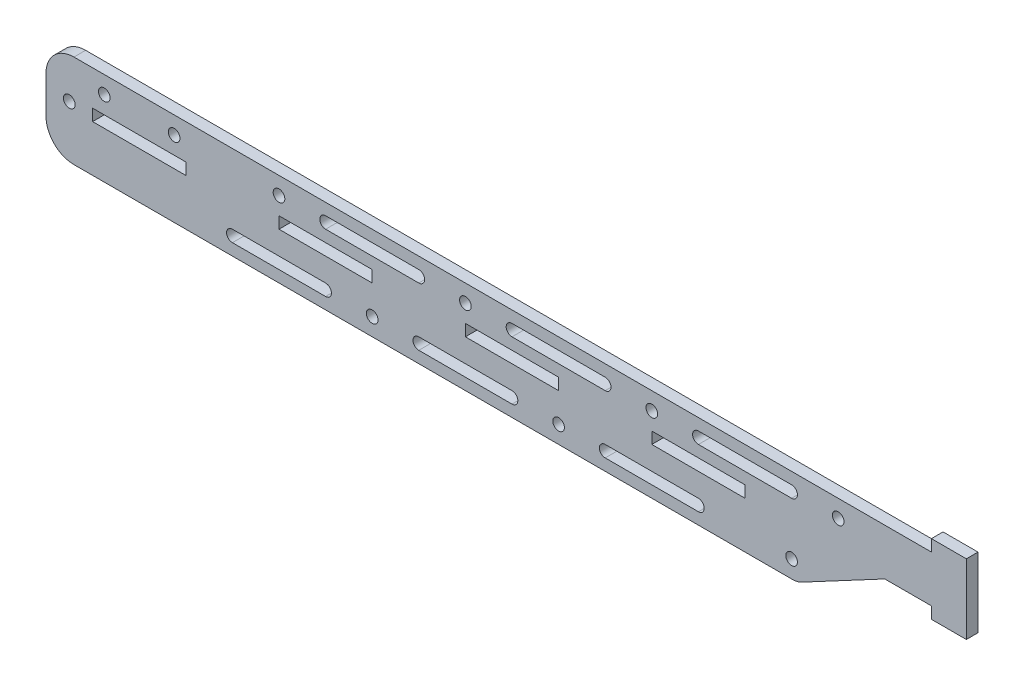
SolidWorks part; units mm, degrees
material "ABS"
ref_plane "Front Plane" through (0, 0, 0) normal (0, 0, 1) x (1, 0, 0)
ref_plane "Top Plane" through (0, 0, 0) normal (0, 1, 0) x (1, 0, 0)
ref_plane "Right Plane" through (0, 0, 0) normal (1, 0, 0) x (0, 0, -1)
sketch "Sketch1" plane through (0, 0, 0) normal (0, 0, 1) x (1, 0, 0)
  line L0 (56.0647, 20.279) -> (-234.1952, 20.279) construction
  line L1 (68.7647, 20.279) -> (56.0647, 20.279)
  line L2 (-159.8353, 20.279) -> (-134.4353, 20.279)
  line L3 (-152.2153, 32.979) -> (68.7647, 32.979)
  line L4 (68.7647, 32.979) -> (68.7647, 36.154)
  line L5 (68.7647, 36.154) -> (78.2897, 36.154)
  line L6 (78.2897, 36.154) -> (78.2897, 17.104)
  line L7 (-134.4353, 20.279) -> (-134.4353, 23.454)
  line L8 (-159.8353, 23.454) -> (-159.8353, 20.279)
  line L9 (-134.4353, 23.454) -> (-159.8353, 23.454)
  line L10 (-109.0353, 23.454) -> (-109.0353, 20.279)
  line L11 (-109.0353, 20.279) -> (-83.6353, 20.279)
  line L12 (-109.0353, 23.454) -> (-83.6353, 23.454)
  line L13 (-83.6353, 23.454) -> (-83.6353, 20.279)
  line L14 (-58.2353, 23.454) -> (-58.2353, 20.279)
  line L15 (-58.2353, 23.454) -> (-32.8353, 23.454)
  line L16 (-32.8353, 23.454) -> (-32.8353, 20.279)
  line L17 (-58.2353, 20.279) -> (-32.8353, 20.279)
  line L18 (-7.4353, 23.454) -> (-7.4353, 20.279)
  line L19 (-7.4353, 23.454) -> (17.9647, 23.454)
  line L20 (17.9647, 23.454) -> (17.9647, 20.279)
  line L21 (-7.4353, 20.279) -> (17.9647, 20.279)
  line L22 (-152.2153, 7.579) -> (30.9822, 7.579)
  line L23 (78.2897, 17.104) -> (68.7647, 17.104)
  line L24 (68.7647, 17.104) -> (68.7647, 20.279)
  line L25 (-159.8353, 21.8665) -> (-166.1853, 21.8665) construction
  line L26 (56.0647, 20.279) -> (33.3728, 8.1766)
  line L27 (-152.2153, 32.979) -> (-164.9153, 32.979)
  line L28 (-147.1353, 23.454) -> (-147.1353, 28.2165) construction
  line L29 (-166.1853, 23.454) -> (-166.1853, 20.279) construction
  line L30 (-172.5353, 23.454) -> (-172.5353, 25.359)
  line L31 (-172.5353, 15.199) -> (-172.5353, 23.454)
  line L32 (-152.2153, 7.579) -> (-164.9153, 7.579)
  line L33 (-109.0353, 28.2165) -> (-147.1353, 28.2165) construction
  line L34 (-147.1353, 28.2165) -> (-156.6603, 28.2165) construction
  line L45 (5.2647, 29.804) -> (30.6647, 29.804)
  line L53 (-45.5353, 13.929) -> (-70.9353, 13.929)
  line L54 (-96.3353, 13.929) -> (-121.7353, 13.929)
  line L55 (-121.7353, 10.754) -> (-96.3353, 10.754)
  line L56 (-70.9353, 10.754) -> (-45.5353, 10.754)
  line L60 (5.2647, 13.929) -> (-20.1353, 13.929)
  line L61 (-20.1353, 10.754) -> (5.2647, 10.754)
  line L64 (30.6647, 26.629) -> (5.2647, 26.629)
  line L66 (81.4647, 10.754) -> (106.8647, 10.754) [skipped]
  line L67 (106.8647, 13.929) -> (81.4647, 13.929) [skipped]
  line L70 (-45.5353, 29.804) -> (-20.1353, 29.804)
  line L71 (-96.3353, 29.804) -> (-70.9353, 29.804)
  line L72 (-70.9353, 26.629) -> (-96.3353, 26.629)
  line L73 (-20.1353, 26.629) -> (-45.5353, 26.629)
  line L77 (56.0647, 29.804) -> (81.4647, 29.804) [skipped]
  line L78 (81.4647, 26.629) -> (56.0647, 26.629) [skipped]
  line L79 (56.0647, 13.929) -> (30.6647, 13.929) [skipped]
  line L80 (30.6647, 10.754) -> (56.0647, 10.754) [skipped]
  circle A0 centre (30.6647, 12.3415) radius 1.5875
  arc A1 (33.3728, 8.1766) -> (30.9822, 7.579) centre (30.9822, 12.659) cw
  circle A2 centre (-109.0353, 28.2165) radius 1.5875
  arc A3 (-172.5353, 25.359) -> (-164.9153, 32.979) centre (-164.9153, 25.359) cw
  arc A4 (-164.9153, 7.579) -> (-172.5353, 15.199) centre (-164.9153, 15.199) cw
  circle A5 centre (-166.1853, 21.8665) radius 1.5875
  circle A6 centre (-109.0353, 28.2165) radius 3.175 construction
  circle A7 centre (-156.6603, 28.2165) radius 1.5875
  circle A8 centre (-137.6103, 28.2165) radius 1.5875
  circle A13 centre (-83.6353, 12.3415) radius 1.5875
  arc A14 (-121.7353, 13.929) -> (-121.7353, 10.754) centre (-121.7353, 12.3415) ccw
  arc A15 (-96.3353, 10.754) -> (-96.3353, 13.929) centre (-96.3353, 12.3415) ccw
  circle A16 centre (-32.8353, 12.3415) radius 1.5875
  arc A17 (-70.9353, 13.929) -> (-70.9353, 10.754) centre (-70.9353, 12.3415) ccw
  arc A18 (-45.5353, 10.754) -> (-45.5353, 13.929) centre (-45.5353, 12.3415) ccw
  arc A20 (-20.1353, 13.929) -> (-20.1353, 10.754) centre (-20.1353, 12.3415) ccw
  arc A21 (5.2647, 10.754) -> (5.2647, 13.929) centre (5.2647, 12.3415) ccw
  circle A26 centre (-58.2353, 28.2165) radius 1.5875
  arc A27 (30.6647, 29.804) -> (30.6647, 26.629) centre (30.6647, 28.2165) cw
  arc A28 (81.4647, 13.929) -> (81.4647, 10.754) centre (81.4647, 12.3415) ccw [skipped]
  arc A29 (106.8647, 10.754) -> (106.8647, 13.929) centre (106.8647, 12.3415) ccw [skipped]
  arc A30 (5.2647, 26.629) -> (5.2647, 29.804) centre (5.2647, 28.2165) cw
  circle A33 centre (-7.4353, 28.2165) radius 1.5875
  circle A34 centre (43.3647, 28.2165) radius 1.5875
  arc A35 (-20.1353, 29.804) -> (-20.1353, 26.629) centre (-20.1353, 28.2165) cw
  arc A36 (-45.5353, 26.629) -> (-45.5353, 29.804) centre (-45.5353, 28.2165) cw
  arc A38 (-70.9353, 29.804) -> (-70.9353, 26.629) centre (-70.9353, 28.2165) cw
  arc A39 (-96.3353, 26.629) -> (-96.3353, 29.804) centre (-96.3353, 28.2165) cw
  circle A42 centre (68.7647, 12.3415) radius 1.5875 [skipped]
  arc A43 (81.4647, 29.804) -> (81.4647, 26.629) centre (81.4647, 28.2165) cw [skipped]
  arc A44 (56.0647, 26.629) -> (56.0647, 29.804) centre (56.0647, 28.2165) cw [skipped]
  arc A45 (56.0647, 10.754) -> (56.0647, 13.929) centre (56.0647, 12.3415) ccw [skipped]
  arc A46 (30.6647, 13.929) -> (30.6647, 10.754) centre (30.6647, 12.3415) ccw [skipped]
  circle A47 centre (17.9647, 12.3415) radius 1.5875 [skipped]
  point P41 (-159.8353, 32.979)
  point P44 (-159.8353, 7.579)
  dimension "D4" = 3.175
  dimension "D6" = 3.175
  dimension "D7" = 19.05
  dimension "D9" = 9.525
  dimension "D10" = 3.175
  dimension "D11" = 12.7
  dimension "D12" = 3.175
  dimension "D13" = 5.08
  dimension "D15" = 12.7
  dimension "D19" = 3.175
  dimension "D20" = 6.35
  dimension "D5" = 25.4
  dimension "D14" = 12.7
  dimension "D33" = 5
  dimension "D35" = 3.175
  dimension "D38" = 3.175
  dimension "D21" = 9.525
  dimension "D16" = 7.62
  dimension "D18" = 7.62
  dimension "D22" = 3.175
  dimension "D2" = 25.4
  dimension "D8" = 3.175
  dimension "D17" = 12.7
  dimension "D36" = 4
  dimension "D37" = 3
  dimension "D39" = 3
extrude "Boss-Extrude1" add sketch "Sketch1" along normal blind 3.175
